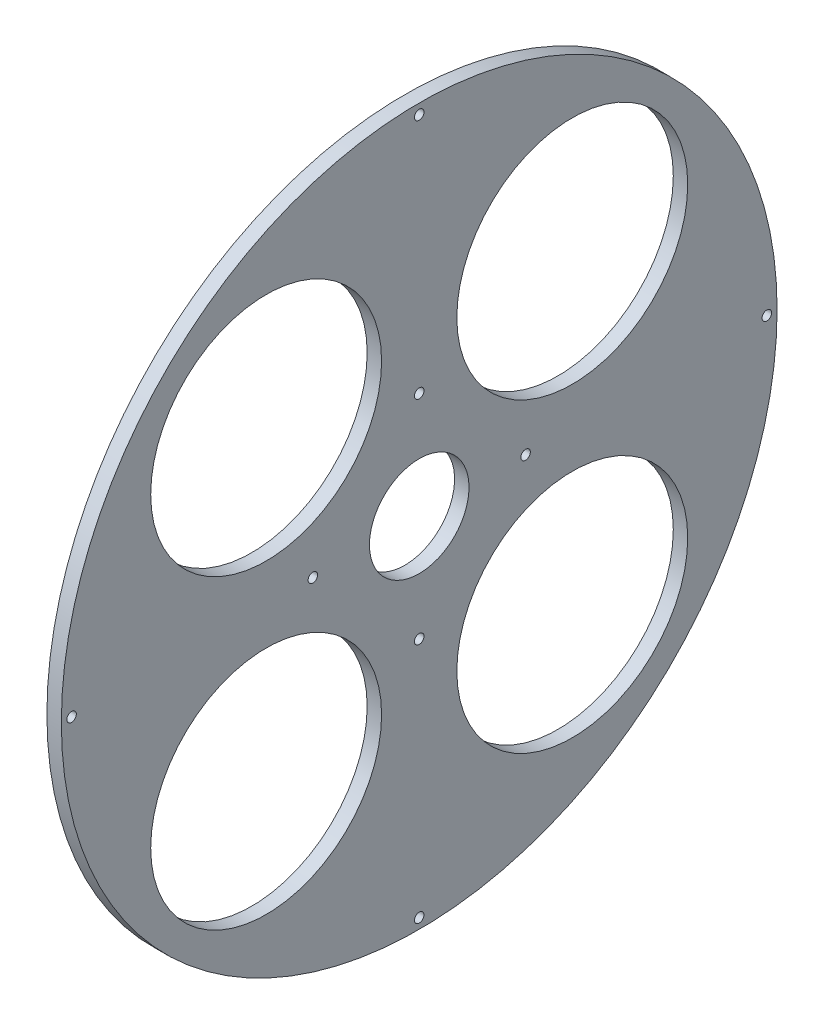
SolidWorks part; units mm, degrees
material "ABS"
ref_plane "Plano frontal" through (0, 0, 0) normal (0, 0, 1) x (1, 0, 0)
ref_plane "Plano superior" through (0, 0, 0) normal (0, 1, 0) x (1, 0, 0)
ref_plane "Plano direito" through (0, 0, 0) normal (1, 0, 0) x (0, 0, -1)
sketch "Esboço1" plane through (0, 0, 0) normal (0, 0, 1) x (1, 0, 0)
  line L0 (0, 0) -> (0, 248) construction
  line L1 (-5, 248) -> (5, 248)
  line L4 (5, 248) -> (5, 34.5)
  line L6 (0, 0) -> (68.8135, 0) construction
  line L7 (-5, 248) -> (-5, 34.5)
  line L10 (5, 34.5) -> (-5, 34.5)
  dimension "D1" = 496
  dimension "D3" = 10
  dimension "D5" = 69
revolve "Revolução1" add sketch "Esboço1" angle 360 about L6
hole_wizard "Furo com folga de M61" positions "Esboço3" profile "Esboço4" hole size "M6" standard "Ansi Metric"
sketch "Esboço3" plane through (-18.8, 0, 0) normal (-1, 0, 0) x (0, 0, 1)
  line L0 (0, 52) -> (0, 95.4) construction
  circle A2 centre (0, 0) radius 73.7 construction
  point P0 (0, 73.7)
  point P17 (73.7, 0)
  point P18 (0, -73.7)
  point P19 (-73.7, 0)
  point P20 (0, 0)
sketch "Esboço4" plane through (-18.8, 73.7, 0) normal (0, 1, 0) x (0, 0, 1)
  line L0 (0, 0) -> (0, 25.7818)
  line L1 (0, 25.7818) -> (3.3, 23.799)
  line L2 (3.3, 23.799) -> (3.3, 0)
  line L3 (3.3, 0) -> (0, 0)
  line L4 (0, 25.7818) -> (-3.3, 23.799) construction
  line L5 (0, -6.35) -> (0, 107.95) construction
  dimension "Hole Dia." = 6.6
  dimension "Hole Depth" = 23.799
  dimension "Drill Angle" = 118
sketch "Esboço7" plane through (-5, 0, 0) normal (-1, 0, 0) x (0, 0, 1)
  line L0 (0, 0) -> (0, 248) construction
  line L1 (0, 0) -> (248, 0) construction
  line L2 (0, 0) -> (175.3625, 175.3625) construction
  circle A0 centre (0, 0) radius 248 construction
  circle A1 centre (106.066, 106.066) radius 80
  circle A2 centre (106.066, -106.066) radius 80
  circle A3 centre (-106.066, -106.066) radius 80
  circle A4 centre (-106.066, 106.066) radius 80
  circle A6 centre (0, 0) radius 150 construction
  dimension "D2" = 160
  dimension "D1" = 45
  dimension "D3" = 150
  dimension "D4" = 4
extrude "Corte-extrusão1" cut sketch "Esboço7" against normal through all
hole_wizard "Furo com folga de M62" positions "Esboço8" profile "Esboço9" hole size "M6" standard "Ansi Metric"
sketch "Esboço8" plane through (14.3436, 0, 0) normal (1, 0, 0) x (0, 0, -1)
  line L0 (0, 248.8953) -> (0, 232.8953) construction
  point P9 (0, 240.8953)
  point P14 (240.8953, 0)
  point P15 (0, -240.8953)
  point P16 (-240.8953, 0)
  point P17 (0, 0)
sketch "Esboço9" plane through (14.3436, 240.8953, 0) normal (0, 1, 0) x (0, 0, -1)
  line L0 (0, 0) -> (0, 21.3255)
  line L1 (0, 21.3255) -> (3.3, 19.3426)
  line L2 (3.3, 19.3426) -> (3.3, 0)
  line L3 (3.3, 0) -> (0, 0)
  line L4 (0, 21.3255) -> (-3.3, 19.3426) construction
  line L5 (0, -6.35) -> (0, 107.95) construction
  dimension "Hole Dia." = 6.6
  dimension "Hole Depth" = 19.3426
  dimension "Drill Angle" = 118
